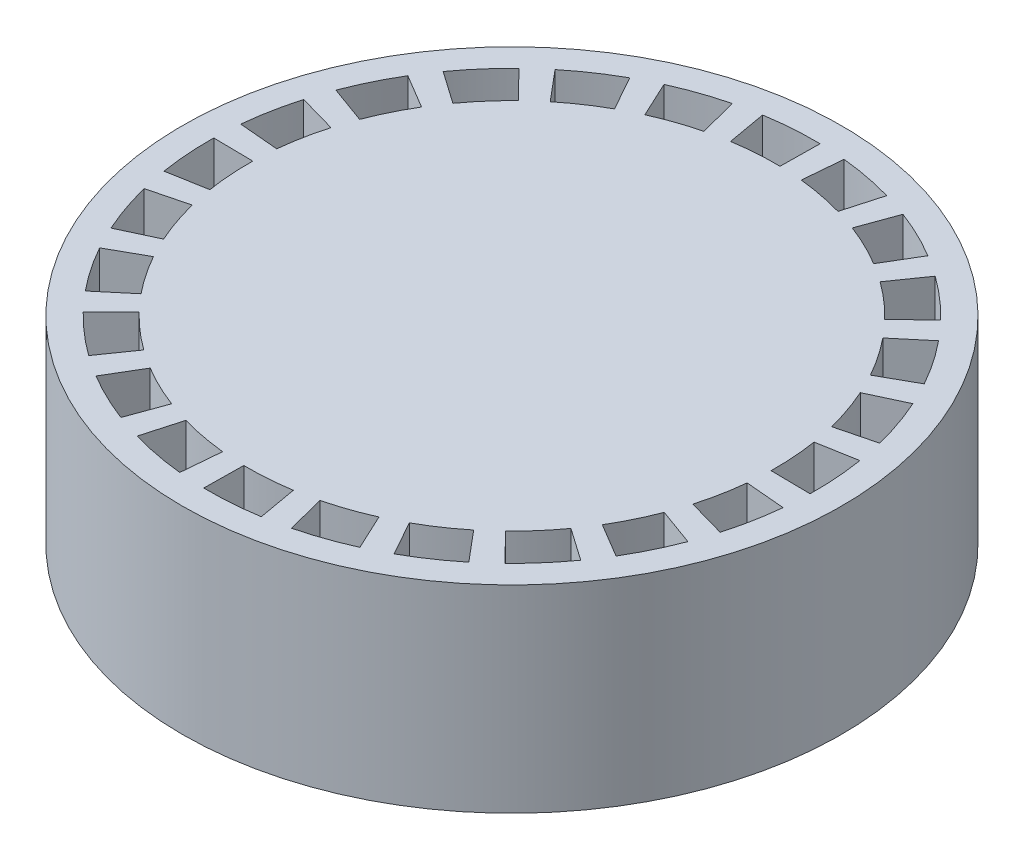
SolidWorks part; units mm, degrees
ref_plane "Front Plane" through (0, 0, 0) normal (0, 0, 1) x (1, 0, 0)
ref_plane "Top Plane" through (0, 0, 0) normal (0, 1, 0) x (1, 0, 0)
ref_plane "Right Plane" through (0, 0, 0) normal (1, 0, 0) x (0, 0, -1)
sketch "Sketch1" plane through (0, 0, 0) normal (0, 1, 0) x (1, 0, 0)
  circle A0 centre (0, 0) radius 31.75
extrude "Boss-Extrude1" add sketch "Sketch1" along normal blind 19.05
sketch "Sketch2" plane through (0, 19.05, 0) normal (0, 1, 0) x (1, 0, 0)
  line L0 (0.4319, 25.3963) -> (0.4816, 29.206)
  line L1 (-4.0214, 25.0796) -> (-4.6853, 28.8318)
  arc A0 (0.4816, 29.206) -> (-4.6853, 28.8318) centre (0, 0) ccw
  arc A1 (0.4319, 25.3963) -> (-4.0214, 25.0796) centre (0, 0) ccw
  circle A2 centre (0, 0) radius 31.75 construction
extrude "Cut-Extrude1" cut sketch "Sketch2" against normal blind 5.08
sketch "Sketch3" plane through (0, 0, 0) normal (1, 0, 0) x (0, 0, -1)
  line L0 (0, 0) -> (0, 127.9218) construction
pattern_circular "CirPattern1" count 24 every 15 about axis through (0, 0, 0) along (0, 1, 0) of "Cut-Extrude1"
